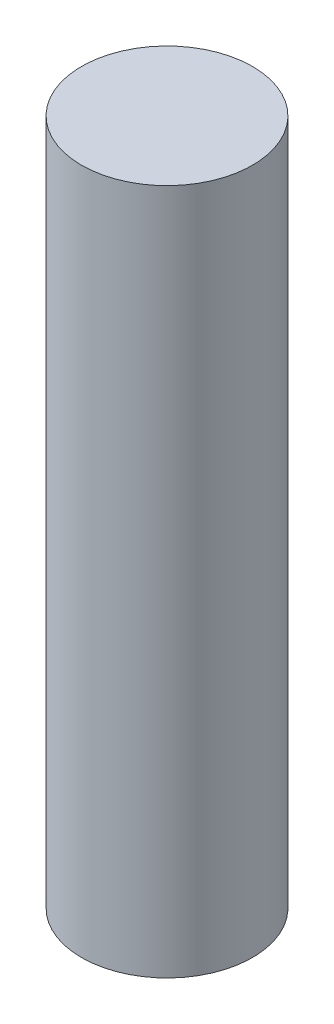
SolidWorks part; units mm, degrees
ref_plane "Front Plane" through (0, 0, 0) normal (0, 0, 1) x (1, 0, 0)
ref_plane "Top Plane" through (0, 0, 0) normal (0, 1, 0) x (1, 0, 0)
ref_plane "Right Plane" through (0, 0, 0) normal (1, 0, 0) x (0, 0, -1)
sketch "Sketch3" plane through (0, 0, 0) normal (0, 1, 0) x (1, 0, 0)
  circle A0 centre (0, 0) radius 0.935
  dimension "D1" = 1.87
extrude "Boss-Extrude1" add sketch "Sketch3" along normal blind 7.5
